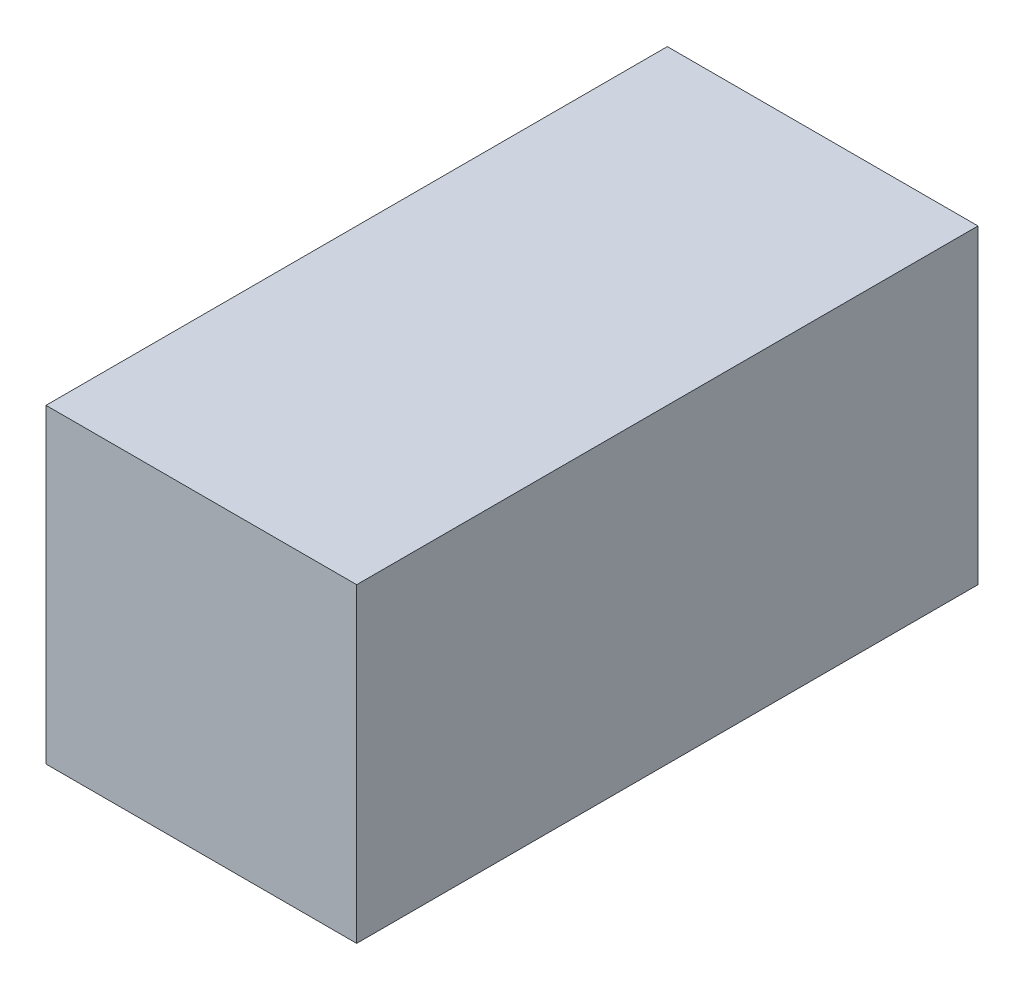
SolidWorks part; units mm, degrees
ref_plane "Plan de face" through (0, 0, 0) normal (0, 0, 1) x (1, 0, 0)
ref_plane "Plan de dessus" through (0, 0, 0) normal (0, 1, 0) x (1, 0, 0)
ref_plane "Plan de droite" through (0, 0, 0) normal (1, 0, 0) x (0, 0, -1)
sketch "Esquisse1" plane through (0, 0, 0) normal (0, 0, 1) x (1, 0, 0)
  line L1 (0, 0) -> (-10, 0)
  line L2 (0, 0) -> (0, 10)
  line L3 (0, 10) -> (-10, 10)
  line L4 (-10, 0) -> (-10, 10)
  dimension "D1" = 10
extrude "Boss.-Extru.1" add sketch "Esquisse1" along normal blind 20
sketch "Esquisse2" [suppressed] plane through (0, 0, 0) normal (0, 0, -1) x (-1, 0, 0)
  line L8 (-3, -3) -> (13, -3)
  line L9 (13, -3) -> (13, 13)
  line L10 (13, 13) -> (-3, 13)
  line L11 (-3, 13) -> (-3, -3)
  line L12 (-3, -3) -> (13, -3)
  line L13 (13, -3) -> (13, 13)
  line L14 (13, 13) -> (-3, 13)
  line L15 (-3, 13) -> (-3, -3)
  dimension "D1" = 3
extrude "Boss.-Extru.2" [suppressed] add sketch "Esquisse2" against normal blind 5
sketch "Esquisse3" [suppressed] plane through (0, 0, 20) normal (0, 0, 1) x (1, 0, 0)
  line L4 (-13, -3) -> (3, -3)
  line L5 (-13, 13) -> (-13, -3)
  line L6 (3, 13) -> (-13, 13)
  line L7 (3, -3) -> (3, 13)
  line L8 (-13, -3) -> (3, -3)
  line L9 (-13, 13) -> (-13, -3)
  line L10 (3, 13) -> (-13, 13)
  line L11 (3, -3) -> (3, 13)
  dimension "D1" = 0
extrude "Boss.-Extru.3" [suppressed] add sketch "Esquisse3" against normal blind 5
